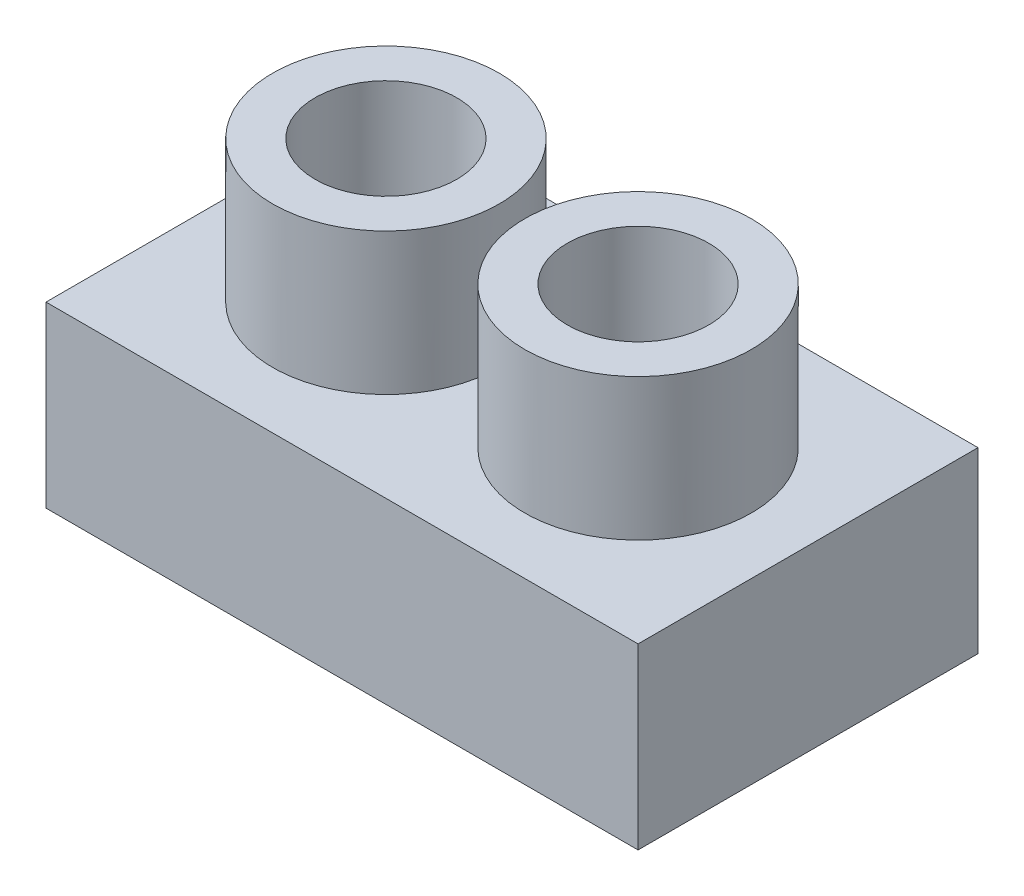
SolidWorks part; units mm, degrees
ref_plane "Front Plane" through (0, 0, 0) normal (0, 0, 1) x (1, 0, 0)
ref_plane "Top Plane" through (0, 0, 0) normal (0, 1, 0) x (1, 0, 0)
ref_plane "Right Plane" through (0, 0, 0) normal (1, 0, 0) x (0, 0, -1)
sketch "Sketch1" plane through (0, 0, 0) normal (0, 1, 0) x (1, 0, 0)
  line L1 (-10.45, -6) -> (10.45, -6)
  line L2 (-10.45, -6) -> (-10.45, 6)
  line L3 (-10.45, 6) -> (10.45, 6)
  line L4 (10.45, -6) -> (10.45, 6)
  line L5 (-10.45, -6) -> (10.45, 6) construction
  line L6 (-10.45, 6) -> (10.45, -6) construction
  point P0 (0, 0)
  dimension "D1" = 20.9
  dimension "D2" = 12
extrude "Boss-Extrude1" add sketch "Sketch1" along normal blind 6.3
sketch "Sketch2" plane through (0, 6.3, 0) normal (0, 1, 0) x (1, 0, 0)
  line L0 (-10.45, 0) -> (10.45, 0) construction
  line L1 (-10.45, 6) -> (-10.45, -6) construction
  line L2 (10.45, -6) -> (10.45, 6) construction
  circle A0 centre (-4.45, 0) radius 4
  circle A1 centre (4.45, 0) radius 4
  dimension "D1" = 8
  dimension "D2" = 8
  dimension "D3" = 8.9
  dimension "D4" = 4.45
extrude "Boss-Extrude2" add sketch "Sketch2" along normal blind 5
sketch "Sketch3" plane through (0, 11.3, 0) normal (0, 1, 0) x (1, 0, 0)
  circle A11 centre (4.45, 0) radius 2.5
  circle A12 centre (4.45, 0) radius 2.5
  circle A14 centre (-4.45, 0) radius 2.5
  circle A15 centre (-4.45, 0) radius 2.5
  dimension "D1" = 1.5
  dimension "D2" = 1.5
extrude "Cut-Extrude1" cut sketch "Sketch3" against normal up to surface (11.3 mm away) up to face at (0, 0, 0)
